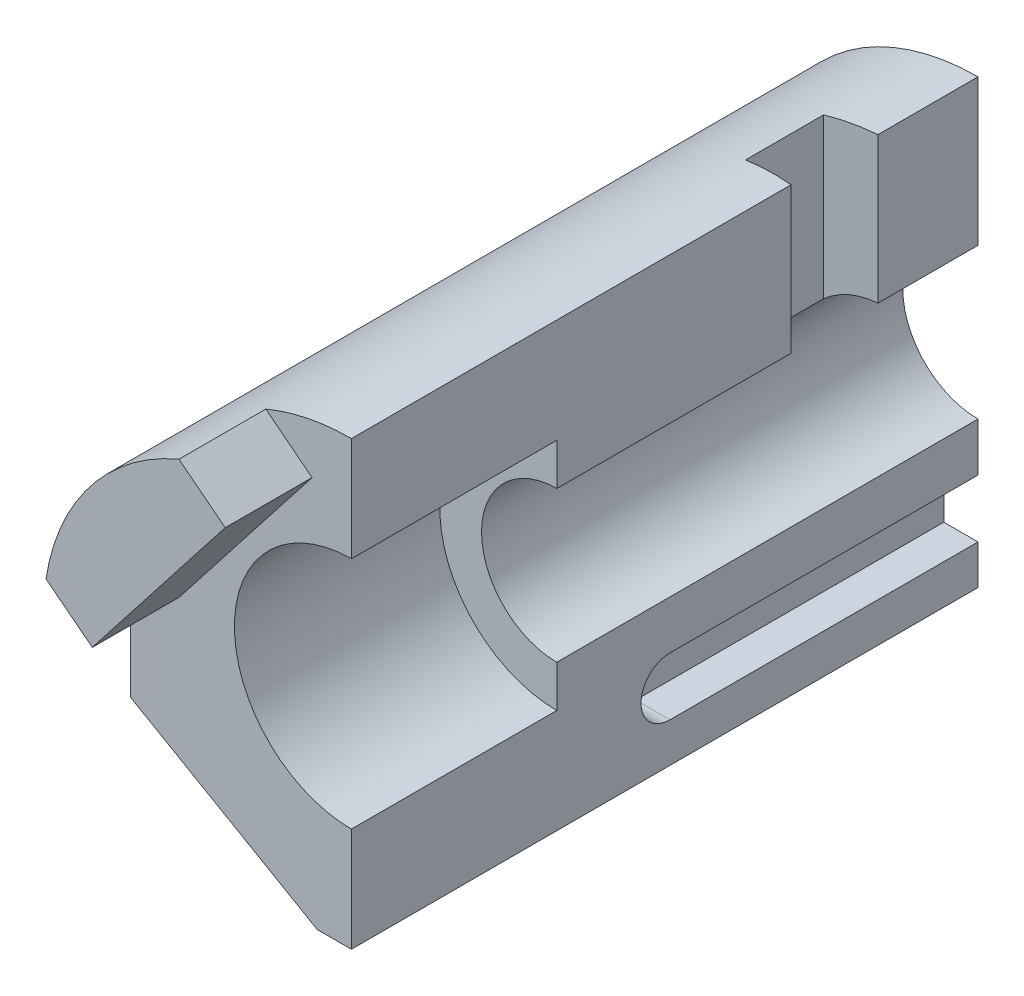
SolidWorks part; units mm, degrees
material "1060 Alloy"
ref_plane "Front Plane" through (0, 0, 0) normal (0, 0, 1) x (1, 0, 0)
ref_plane "Top Plane" through (0, 0, 0) normal (0, 1, 0) x (1, 0, 0)
ref_plane "Right Plane" through (0, 0, 0) normal (1, 0, 0) x (0, 0, -1)
sketch "Sketch5" plane through (0, 0, 0) normal (0, 0, 1) x (1, 0, 0)
  line L0 (-84, -43.0081) -> (-84, 0)
  line L1 (-84, -43.0081) -> (-13, -84)
  line L2 (-13, -84) -> (0, -84)
  line L3 (0, -84) -> (0, -28.575)
  line L4 (0, 28.575) -> (0, 84)
  line L5 (-13, -84) -> (-98.2806, -84) construction
  line L6 (0, 98.179) -> (0, -146.5505) construction
  arc A0 (-84, 0) -> (0, 84) centre (0, 0) cw
  arc A1 (0, -28.575) -> (0, 28.575) centre (0, 0) cw
  dimension "D5" = 28.575
  dimension "D1" = 84
  dimension "D2" = 13
  dimension "D3" = 30
  dimension "D4" = 84
extrude "Boss-Extrude1" add sketch "Sketch5" along normal blind 238
sketch "Sketch6" plane through (0, 0, 238) normal (0, 0, 1) x (1, 0, 0)
  circle A0 centre (0, 0) radius 44.45
  dimension "D1" = 88.9
extrude "Cut-Extrude1" cut sketch "Sketch6" against normal blind 78
sketch "Sketch7" plane through (0, 0, 0) normal (1, 0, 0) x (0, 0, -1)
  line L0 (0, 28.575) -> (0, 84) construction
  line L1 (-71, 86) -> (-38, 86)
  line L2 (-71, 86) -> (-71, 1)
  line L3 (-71, 1) -> (-38, 1)
  line L4 (-38, 86) -> (-38, 1)
  line L6 (-238, 84) -> (0, 84) construction
  dimension "D1" = 33
  dimension "D2" = 38
  dimension "D3" = 85
  dimension "D4" = 2
extrude "Cut-Extrude2" cut sketch "Sketch7" against normal blind 19 draft 5
sketch "Sketch8" plane through (0, 0, 0) normal (1, 0, 0) x (0, 0, -1)
  line L4 (-117, -58) -> (66, -58) construction
  line L5 (-117, -47) -> (66, -47)
  line L6 (-117, -69) -> (66, -69)
  line L7 (-238, -84) -> (0, -84) construction
  line L8 (0, -84) -> (0, -28.575) construction
  arc A1 (-117, -47) -> (-117, -69) centre (-117, -58) ccw
  arc A2 (66, -69) -> (66, -47) centre (66, -58) ccw
  point P2 (-25.5, -58)
  dimension "D1" = 11
  dimension "D2" = 26
  dimension "D3" = 117
  dimension "D4" = 66
extrude "Cut-Extrude3" cut sketch "Sketch8" against normal blind 13
sketch "Sketch9" plane through (0, 0, 238) normal (0, 0, 1) x (1, 0, 0)
  line L0 (-83.0146, 12.8284) -> (-65.4307, -0.9097)
  line L1 (-65.4307, -0.9097) -> (-14.9464, 63.7072)
  line L2 (-14.9464, 63.7072) -> (-32.5304, 77.4453)
  line L3 (0, 0) -> (-132.3858, 103.4311) construction
  line L4 (-13, -84) -> (-173.2571, -84) construction
  arc A0 (0, 84) -> (-84, 0) centre (0, 0) ccw construction
  arc A1 (-32.5304, 77.4453) -> (-83.0146, 12.8284) centre (0, 0) ccw
  point P8 (-66.1929, 51.7156)
  dimension "D1" = 41
  dimension "D2" = 51
  dimension "D3" = 38
extrude "Boss-Extrude2" add sketch "Sketch9" along normal blind 33
sketch "Sketch10" plane through (0, 0, 0) normal (0, 0, 1) x (1, 0, 0)
  line L0 (0, 130.3577) -> (0, -158.1921) construction
ref_plane "Plane1" through (10, 0, 0) normal (1, 0, 0) x (0, 0, -1)
equation "\"A\"= 238"
equation "\"B\"= 117"
equation "\"C\"= 84"
equation "\"D1@Boss-Extrude1\"=\"A\""
equation "\"D3@Sketch8\"=\"B\""
equation "\"D\"=5"
equation "\"D3@Cut-Extrude2\"=\"D\""
